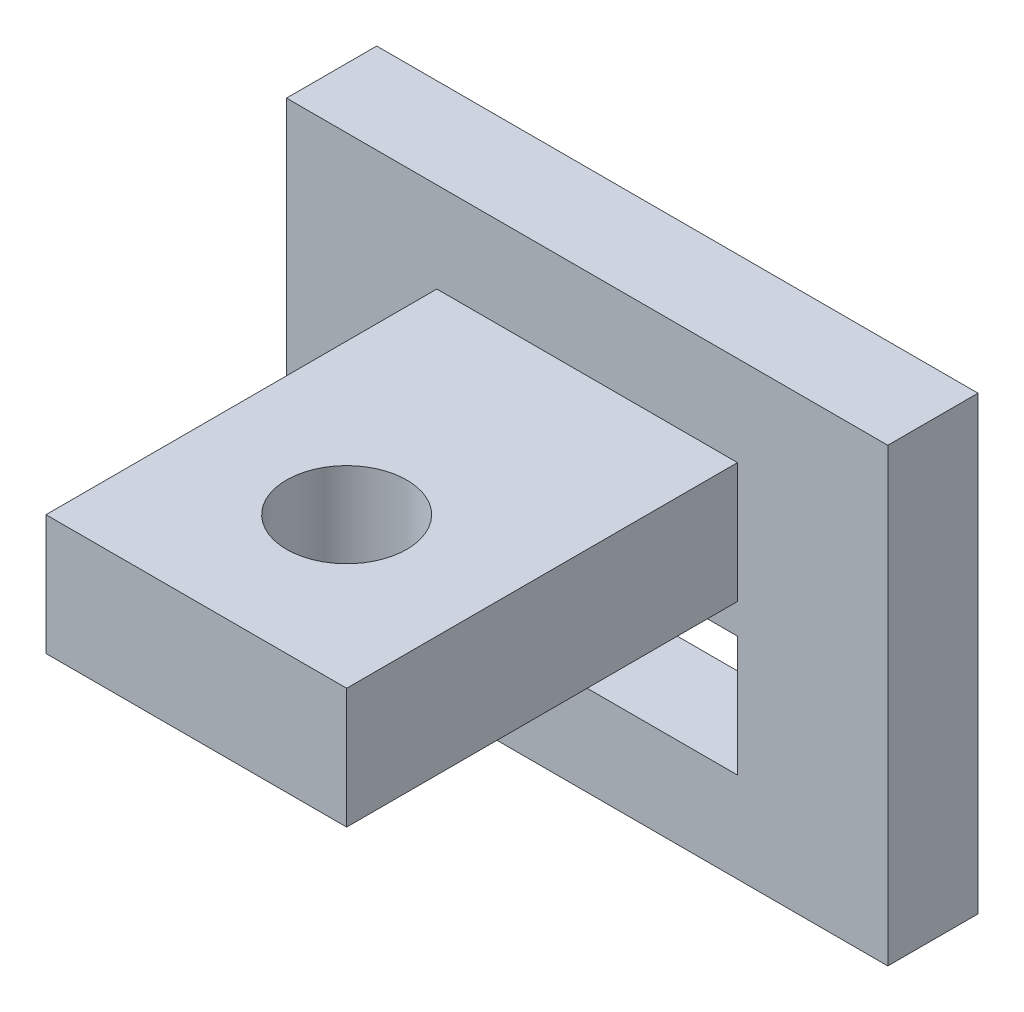
SolidWorks part; units mm, degrees
ref_plane "Front Plane" through (0, 0, 0) normal (0, 0, 1) x (1, 0, 0)
ref_plane "Top Plane" through (0, 0, 0) normal (0, 1, 0) x (1, 0, 0)
ref_plane "Right Plane" through (0, 0, 0) normal (1, 0, 0) x (0, 0, -1)
sketch "Sketch1" plane through (0, 0, 0) normal (0, 0, 1) x (1, 0, 0)
  line L1 (0, 0) -> (-20, 0)
  line L2 (0, 0) -> (0, 15)
  line L3 (0, 15) -> (-20, 15)
  line L4 (-20, 0) -> (-20, 15)
  dimension "D1" = 20
  dimension "D2" = 15
extrude "Boss-Extrude1" add sketch "Sketch1" along normal blind 3
sketch "Sketch2" plane through (0, 0, 3) normal (0, 0, 1) x (1, 0, 0)
  line L0 (0, 15) -> (-20, 15) construction
  line L1 (-15, 12) -> (-5, 12)
  line L2 (-15, 12) -> (-15, 8)
  line L3 (-15, 8) -> (-5, 8)
  line L4 (-5, 12) -> (-5, 8)
  point P4 (-10, 12)
  point P7 (-10, 15)
  dimension "D1" = 10
  dimension "D2" = 4
  dimension "D3" = 3
extrude "Boss-Extrude2" add sketch "Sketch2" along normal blind 13
sketch "Sketch3" plane through (0, 12, 0) normal (0, 1, 0) x (1, 0, 0)
  line L0 (0, -3) -> (-20, -3) construction
  circle A0 centre (-10, -11) radius 2
  point P6 (-10, -3)
  dimension "D1" = 4
  dimension "D2" = 8
sketch "Sketch4" plane through (0, 0, 3) normal (0, 0, 1) x (1, 0, 0)
  line L0 (-15, 12) -> (-15, 8) construction
  line L1 (-15, 7) -> (-5, 7)
  line L2 (-15, 7) -> (-15, 3)
  line L3 (-15, 3) -> (-5, 3)
  line L4 (-5, 7) -> (-5, 3)
  line L5 (-5, 12) -> (-15, 12) construction
  line L6 (0, 15) -> (-20, 15) construction
  line L7 (-15, 8) -> (-5, 8) construction
  point P8 (-10, 7)
  point P11 (-10, 15)
  dimension "D1" = 1
extrude "Cut-Extrude3" cut sketch "Sketch4" against normal through all
extrude "Cut-Extrude4" cut sketch "Sketch3" against normal through all
